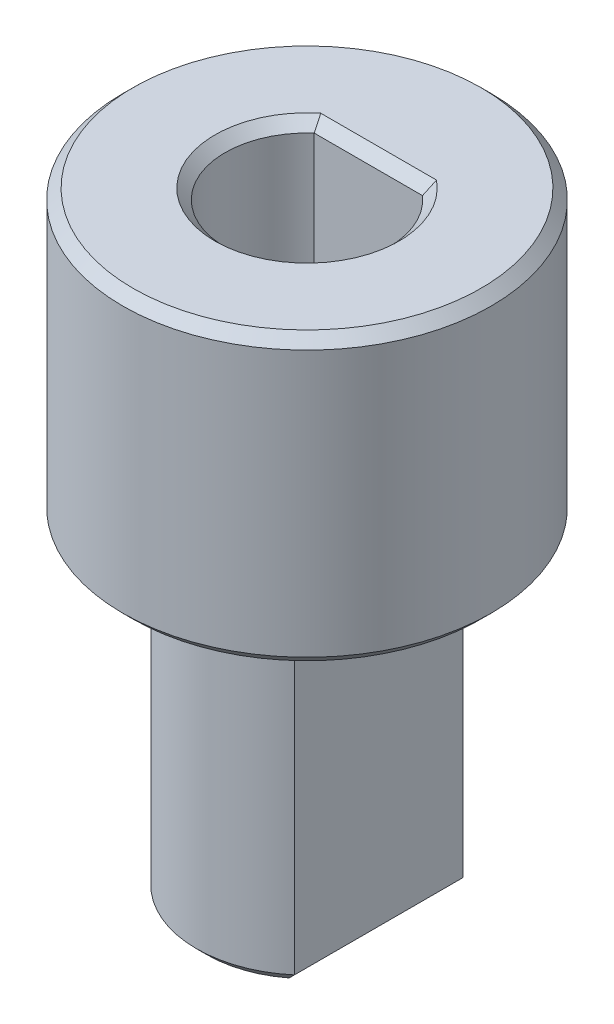
SolidWorks part; units mm, degrees
ref_plane "Front Plane" through (0, 0, 0) normal (0, 0, 1) x (1, 0, 0)
ref_plane "Top Plane" through (0, 0, 0) normal (0, 1, 0) x (1, 0, 0)
ref_plane "Right Plane" through (0, 0, 0) normal (1, 0, 0) x (0, 0, -1)
sketch "Sketch1" plane through (0, 0, 0) normal (0, 1, 0) x (1, 0, 0)
  line L0 (-1.75, 2.0561) -> (-1.75, -2.0561)
  line L1 (1.75, 2.0561) -> (1.75, -2.0561)
  arc A0 (1.75, 2.0561) -> (-1.75, 2.0561) centre (0, 0) ccw
  arc A1 (-1.75, -2.0561) -> (1.75, -2.0561) centre (0, 0) ccw
  dimension "D1" = 5.4
  dimension "D2" = 3.5
  dimension "D3" = 1.75
extrude "Boss-Extrude1" add sketch "Sketch1" along normal blind 8
sketch "Sketch2" plane through (0, 8, 0) normal (0, 1, 0) x (1, 0, 0)
  circle A0 centre (0, 0) radius 4.5
  dimension "D1" = 9
extrude "Boss-Extrude2" add sketch "Sketch2" along normal blind 7 contours A0
sketch "Sketch3" plane through (0, 15, 0) normal (0, 1, 0) x (1, 0, 0)
  line L0 (-1.3229, 1.5) -> (1.3229, 1.5)
  arc A0 (-1.3229, 1.5) -> (1.3229, 1.5) centre (0, 0) ccw
  point P5 (0, -2)
  dimension "D1" = 4
  dimension "D2" = 3.5
extrude "Cut-Extrude1" cut sketch "Sketch3" against normal blind 5.5
fillet "Fillet1" radius 0.5 4 edges at (1.75, 8, 0) (0, 8, 2.7) (-1.75, 8, 0) (0, 8, -2.7)
chamfer "Chamfer1" distance 0.25 angle 45 8 edges at (0, 15, -1.5) (0, 15, 2) (0, 15, 4.5) (0, 8, 4.5) (1.75, 0, 0) (0, 0, 2.7) (-1.75, 0, 0) (0, 0, -2.7)
equation "\"D3@Sketch1\"=\"D2@Sketch1\"/2"
